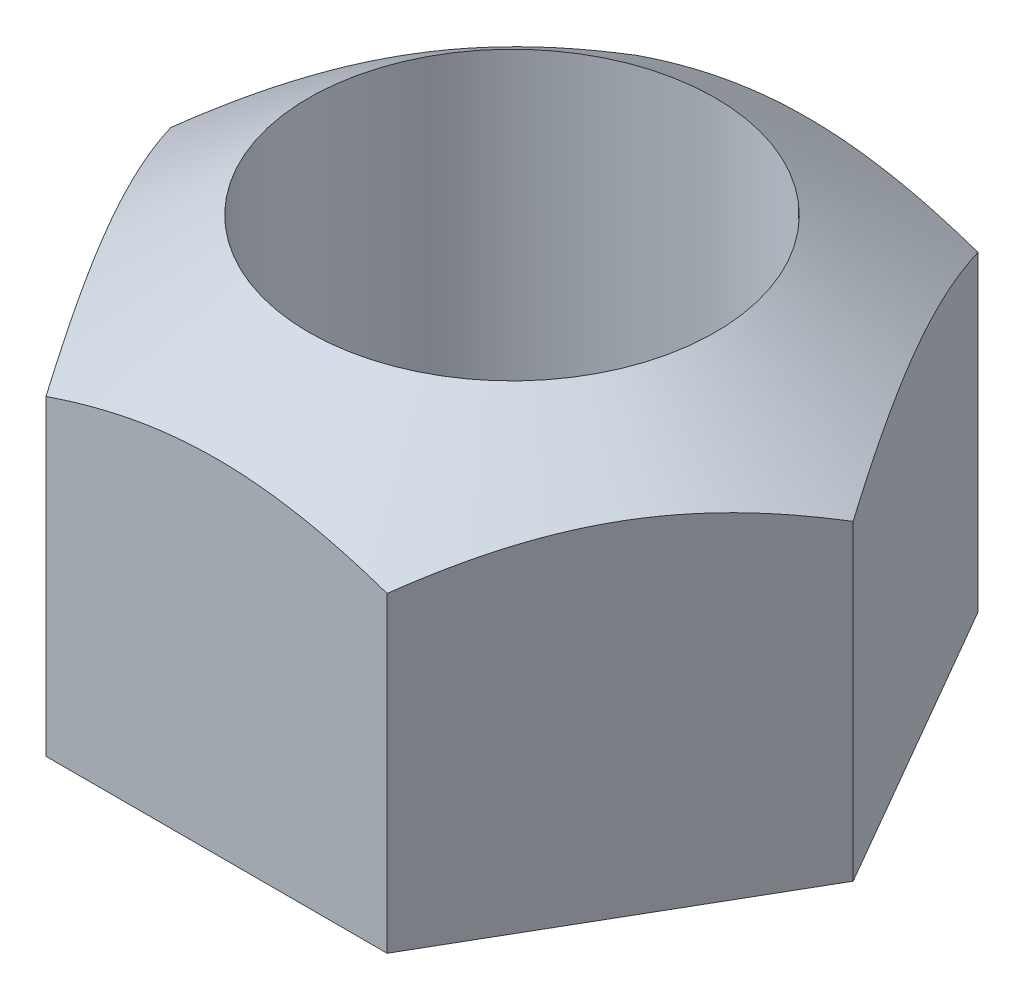
SolidWorks part; units mm, degrees
ref_plane "前视基准面" through (0, 0, 0) normal (0, 0, 1) x (1, 0, 0)
ref_plane "上视基准面" through (0, 0, 0) normal (0, 1, 0) x (1, 0, 0)
ref_plane "右视基准面" through (0, 0, 0) normal (1, 0, 0) x (0, 0, -1)
sketch "草图1" plane through (0, 0, 0) normal (0, 1, 0) x (1, 0, 0)
  line L1 (2.5187, 0) -> (1.2593, 2.1812)
  line L2 (1.2593, 2.1812) -> (-1.2593, 2.1812)
  line L3 (-1.2593, 2.1812) -> (-2.5187, 0)
  line L4 (-2.5187, 0) -> (-1.2593, -2.1812)
  line L5 (-1.2593, -2.1812) -> (1.2593, -2.1812)
  line L6 (1.2593, -2.1812) -> (2.5187, 0)
  circle A0 centre (0, 0) radius 1.5
  circle A1 centre (0, 0) radius 2.5187 construction
extrude "凸台-拉伸1" add sketch "草图1" along normal blind 3
sketch "草图2" plane through (0, 0, 0) normal (0, 0, 1) x (1, 0, 0)
  line L0 (1.5, 3) -> (2.5187, 2.301)
  line L1 (2.5187, 3) -> (2.5187, 0) construction
  line L2 (2.5187, 2.301) -> (2.5187, 3)
  line L3 (2.5187, 3) -> (1.5, 3)
  line L4 (0, 3.3028) -> (0, -0.3863) construction
revolve "切除-旋转1" cut sketch "草图2" angle 360 about L4
scale "缩放比例1" scale about centroid uniform scaling yes scale factor 0.58
move or copy body "实体-移动/复制1" [suppressed] bodies to move or copy 107
